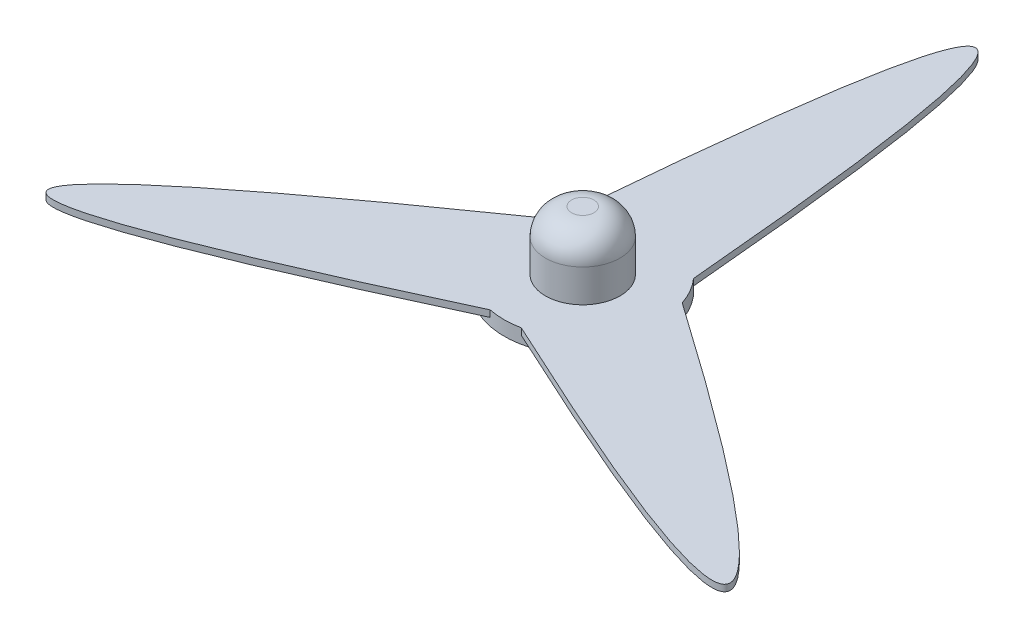
SolidWorks part; units mm, degrees
ref_plane "Front Plane" through (0, 0, 0) normal (0, 0, 1) x (1, 0, 0)
ref_plane "Top Plane" through (0, 0, 0) normal (0, 1, 0) x (1, 0, 0)
ref_plane "Right Plane" through (0, 0, 0) normal (1, 0, 0) x (0, 0, -1)
sketch "Sketch1" plane through (0, 0, 0) normal (0, 1, 0) x (1, 0, 0)
  line L2 (0, 60) -> (0, 300) construction
  arc A0 (-45, 39.6863) -> (-56.8693, 19.128) centre (0, 0) ccw
  circle A1 centre (0, 0) radius 300 construction
  arc A2 (-11.8693, -58.8143) -> (11.8693, -58.8143) centre (0, 0) ccw
  arc A3 (56.8693, 19.128) -> (45, 39.6863) centre (0, 0) ccw
  spline S0 degree 2 poles (-45, 39.6863) (0, 560.3137) (45, 39.6863) knots 0 0 0 1 1 1
  spline S1 degree 2 poles (56.8693, 19.128) (485.2459, -280.1569) (11.8693, -58.8143) knots 0 0 0 1 1 1
  spline S2 degree 2 poles (-11.8693, -58.8143) (-485.2459, -280.1569) (-56.8693, 19.128) knots 0 0 0 1 1 1
  point P17 (0, 0)
  dimension "D1" = 120
  dimension "D2" = 600
  dimension "D3" = 90
extrude "Boss-Extrude1" add sketch "Sketch1" along normal blind 5
sketch "Sketch2" plane through (0, 5, 0) normal (0, 1, 0) x (1, 0, 0)
  circle A0 centre (0, 0) radius 28.5
  dimension "D1" = 57
extrude "Boss-Extrude2" add sketch "Sketch2" along normal blind 45
fillet "Fillet1" radius 20 1 edges at (0, 50, 28.5)
sketch "Sketch3" plane through (0, 0, 0) normal (0, -1, 0) x (1, 0, 0)
  circle A0 centre (0, 0) radius 60
extrude "Boss-Extrude3" add sketch "Sketch3" along normal blind 6
sketch "Sketch4" plane through (0, -6, 0) normal (0, -1, 0) x (1, 0, 0)
  circle A0 centre (0, 0) radius 24
  dimension "D1" = 48
extrude "Cut-Extrude1" cut sketch "Sketch4" against normal blind 36
